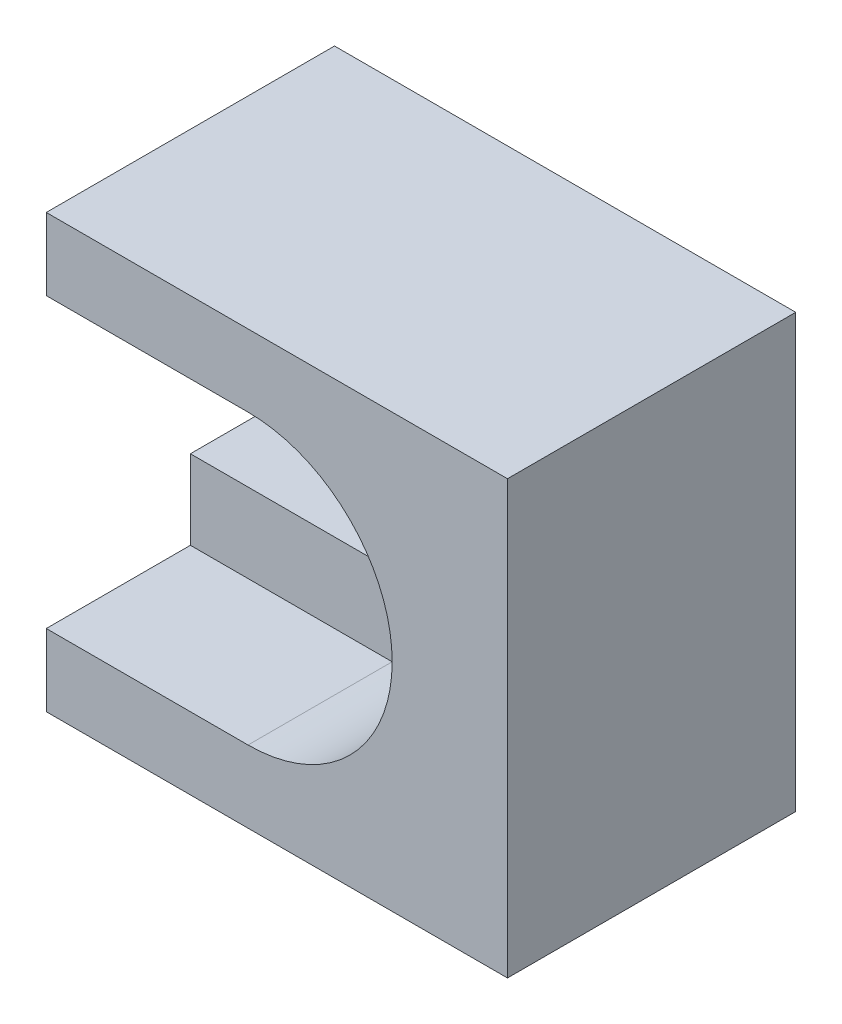
SolidWorks part; units mm, degrees
ref_plane "Ebene vorne" through (0, 0, 0) normal (0, 0, 1) x (1, 0, 0)
ref_plane "Ebene oben" through (0, 0, 0) normal (0, 1, 0) x (1, 0, 0)
ref_plane "Ebene rechts" through (0, 0, 0) normal (1, 0, 0) x (0, 0, -1)
sketch "Skizze1" plane through (0, 0, 0) normal (0, 0, 1) x (1, 0, 0)
  line L1 (0, 0) -> (16, 0)
  line L2 (0, 0) -> (0, 15)
  line L3 (0, 15) -> (16, 15)
  line L4 (16, 0) -> (16, 15)
  dimension "D1" = 15
  dimension "D2" = 16
extrude "Aufsatz-Linear austragen1" add sketch "Skizze1" along normal blind 10
sketch "Skizze2" plane through (0, 0, 10) normal (0, 0, 1) x (1, 0, 0)
  line L0 (0, 7.5) -> (7, 7.5) construction
  line L1 (0, 12.5) -> (7, 12.5)
  line L2 (0, 2.5) -> (7, 2.5)
  line L3 (16, 0) -> (16, 15) construction
  line L4 (0, 15) -> (0, 0) construction
  arc A0 (0, 12.5) -> (0, 2.5) centre (0, 7.5) ccw
  arc A1 (7, 2.5) -> (7, 12.5) centre (7, 7.5) ccw
  point P2 (3.5, 7.5)
  point P9 (16, 7.5)
  dimension "D1" = 5
  dimension "D2" = 7
extrude "Schnitt-Linear austragen1" cut sketch "Skizze2" against normal blind 5
sketch "Skizze3" plane through (0, 0, 5) normal (0, 0, 1) x (1, 0, 0)
  line L0 (0, 7.5) -> (7, 7.5) construction
  line L1 (0, 12.5) -> (0, 2.5) construction
  line L2 (0, 9.75) -> (7, 9.75)
  line L3 (0, 5.25) -> (7, 5.25)
  arc A0 (0, 9.75) -> (0, 5.25) centre (0, 7.5) ccw
  arc A1 (7, 5.25) -> (7, 9.75) centre (7, 7.5) ccw
  point P5 (3.5, 7.5)
  dimension "D1" = 4.5
extrude "Schnitt-Linear austragen2" cut sketch "Skizze3" against normal through all
